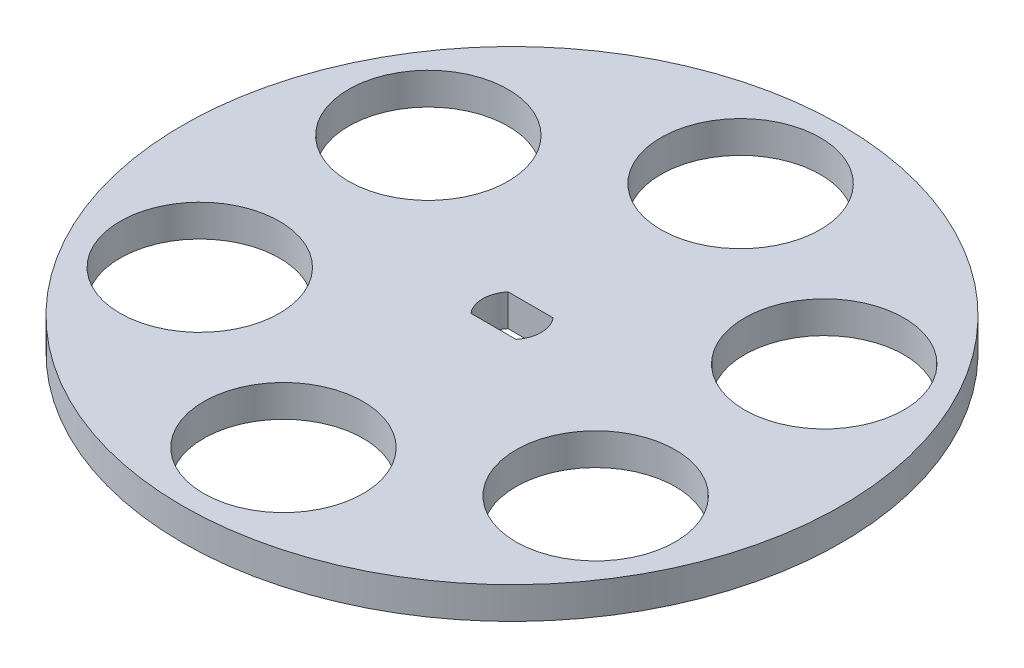
SolidWorks part; units mm, degrees
ref_plane "Front Plane" through (0, 0, 0) normal (0, 0, 1) x (1, 0, 0)
ref_plane "Top Plane" through (0, 0, 0) normal (0, 1, 0) x (1, 0, 0)
ref_plane "Right Plane" through (0, 0, 0) normal (1, 0, 0) x (0, 0, -1)
sketch "Sketch2" plane through (0, 0, 0) normal (0, 1, 0) x (1, 0, 0)
  line L0 (-2.1213, 1.75) -> (2.1213, 1.75)
  line L1 (-2.1213, -1.75) -> (2.1213, -1.75)
  line L2 (-2.75, 0) -> (2.75, 0) construction
  circle A0 centre (0, 0) radius 31
  arc A1 (-2.1213, 1.75) -> (-2.1213, -1.75) centre (0, 0) ccw
  arc A2 (2.1213, -1.75) -> (2.1213, 1.75) centre (0, 0) ccw
  circle A3 centre (0, 21.5) radius 7.5
  circle A7 centre (18.6195, 10.75) radius 7.5
  circle A8 centre (18.6195, -10.75) radius 7.5
  circle A9 centre (0, -21.5) radius 7.5
  circle A10 centre (-18.6195, -10.75) radius 7.5
  circle A11 centre (-18.6195, 10.75) radius 7.5
  point P20 (0, 0)
  point P24 (0, 0)
  dimension "D1" = 62
  dimension "D2" = 5.5
  dimension "D4" = 15
  dimension "D3" = 3.5
  dimension "D5" = 21.5
  dimension "D6" = 6
extrude "Boss-Extrude1" add sketch "Sketch2" along normal blind 3
